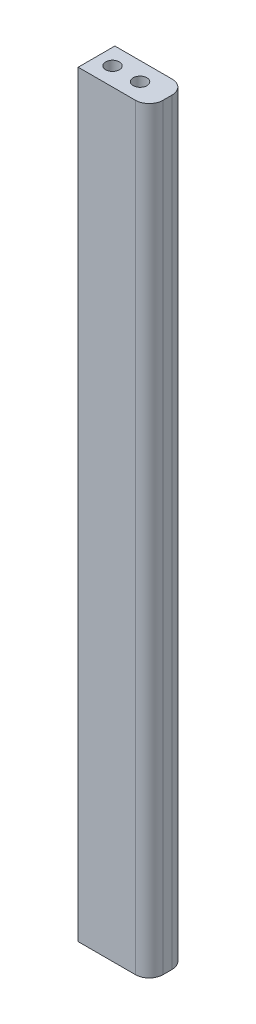
SolidWorks part; units mm, degrees
ref_plane "Front Plane" through (0, 0, 0) normal (0, 0, 1) x (1, 0, 0)
ref_plane "Top Plane" through (0, 0, 0) normal (0, 1, 0) x (1, 0, 0)
ref_plane "Right Plane" through (0, 0, 0) normal (1, 0, 0) x (0, 0, -1)
sketch "Sketch1" plane through (0, 0, 0) normal (0, 1, 0) x (1, 0, 0)
  line L0 (-30.1946, -4.8251) -> (-30.1946, 3.1707)
  line L1 (-30.1946, -4.8251) -> (-17.714, -4.8251)
  line L2 (-19.6372, 3.1707) -> (-17.714, 3.1707)
  line L3 (-14.714, 0.1707) -> (-14.714, -1.8251)
  line L4 (-19.6372, 3.1707) -> (-30.1946, 3.1707)
  circle A0 centre (-20.714, -0.8251) radius 1.5
  circle A1 centre (-26.714, -0.8251) radius 1.5
  arc A2 (-14.714, 0.1707) -> (-17.714, 3.1707) centre (-17.714, 0.1707) ccw
  arc A3 (-14.714, -1.8251) -> (-17.714, -4.8251) centre (-17.714, -1.8251) cw
extrude "Boss-Extrude1" add sketch "Sketch1" along normal blind 165
